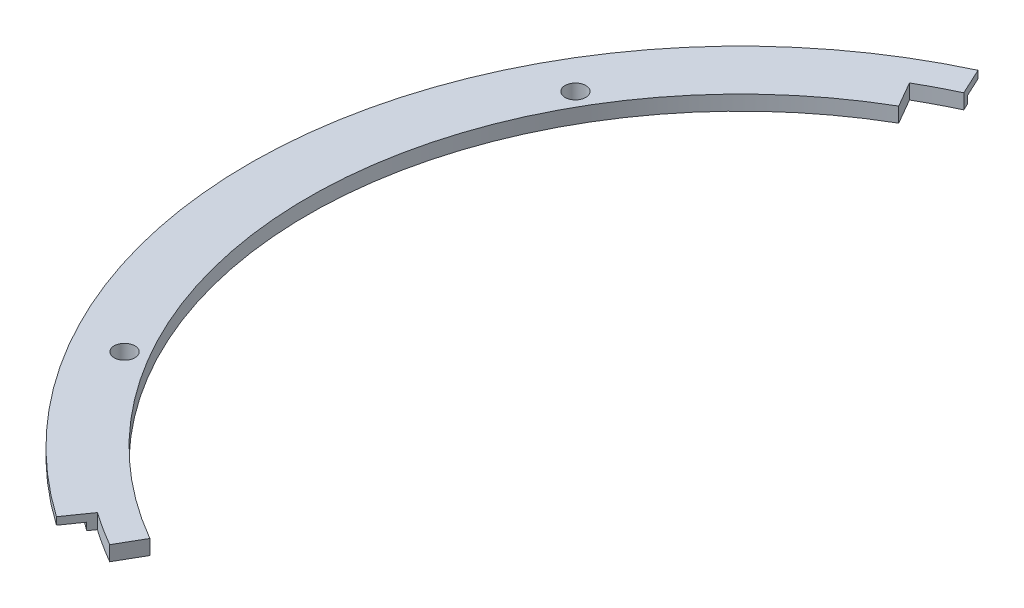
SolidWorks part; units mm, degrees
ref_plane "Front Plane" through (0, 0, 0) normal (0, 0, 1) x (1, 0, 0)
ref_plane "Top Plane" through (0, 0, 0) normal (0, 1, 0) x (1, 0, 0)
ref_plane "Right Plane" through (0, 0, 0) normal (1, 0, 0) x (0, 0, -1)
sketch "Sketch1" plane through (0, 0, 0) normal (0, 1, 0) x (1, 0, 0)
  line L0 (0, 154.5) -> (0, 0) construction
  line L1 (0, 160.85) -> (0, 148.15) construction
  line L2 (0, -55) -> (0, 55) construction
  circle A0 centre (0, 0) radius 154.5 construction
  circle A1 centre (0, 154.5) radius 3.556
  circle A2 centre (133.8009, 77.25) radius 3.556
  circle A3 centre (133.8009, -77.25) radius 3.556
  circle A4 centre (0, -154.5) radius 3.556
  circle A5 centre (-133.8009, -77.25) radius 3.556
  circle A6 centre (-133.8009, 77.25) radius 3.556
  circle A7 centre (0, 0) radius 160.85
  circle A8 centre (0, 0) radius 148.15
  point P17 (0, 0)
  point P20 (0, 154.5)
  dimension "D1" = 7.112
  dimension "D2" = 309
  dimension "D6" = 12.7
  dimension "D4" = 60
  dimension "D5" = 60
  dimension "D3" = 6
extrude "Boss-Extrude1" add sketch "Sketch1" along normal blind 5.08
sketch "Sketch2" plane through (0, 5.08, 0) normal (0, 1, 0) x (1, 0, 0)
  circle A0 centre (0, 0) radius 168.275
  circle A1 centre (0, 0) radius 160.85
  circle A2 centre (0, 0) radius 160.85 construction
  dimension "D1" = 336.55
extrude "Boss-Extrude2" add sketch "Sketch2" against normal blind 2.54
sketch "Sketch3" plane through (0, 5.08, 0) normal (0, 1, 0) x (1, 0, 0)
  line L0 (-88.9, 153.9793) -> (-84.1375, 145.7304)
  line L1 (0, 0) -> (-79.1063, -137.016)
  line L2 (-2.794, 0) -> (2.794, 0) construction
  line L3 (0, 0) -> (-75.1415, 161.1415) construction
  line L4 (0, 0) -> (-96.5186, -137.8428) construction
  line L5 (-62.6109, 134.2695) -> (-71.1161, 152.5089) construction
  line L6 (-96.5186, -137.8428) -> (-84.9753, -121.3574) construction
  line L7 (-79.1062, 137.016) -> (0, 0)
  line L8 (-84.1375, -145.7304) -> (-88.9, -153.9793)
  line L9 (-71.1161, 152.5089) -> (-66.8635, 143.3892)
  line L10 (-90.747, -129.6001) -> (-96.5186, -137.8428)
  circle A0 centre (0, 0) radius 148.15 construction
  circle A1 centre (0, 0) radius 168.275 construction
  arc A2 (-66.8635, 143.3892) -> (-79.1062, 137.016) centre (0, 0) ccw
  arc A3 (-71.1161, 152.5089) -> (-84.1375, 145.7304) centre (0, 0) ccw
  arc A4 (-88.9, 153.9793) -> (-88.9, -153.9793) centre (0, 0) cw
  arc A5 (-84.1375, -145.7304) -> (-96.5186, -137.8428) centre (0, 0) cw
  arc A6 (-90.747, -129.6001) -> (-79.1063, -137.016) centre (0, 0) ccw
  dimension "D2" = 60
  dimension "D3" = 177.8
  dimension "D1" = 120
  dimension "D4" = 5
  dimension "D5" = 5
extrude "Cut-Extrude1" cut sketch "Sketch3" against normal through all
